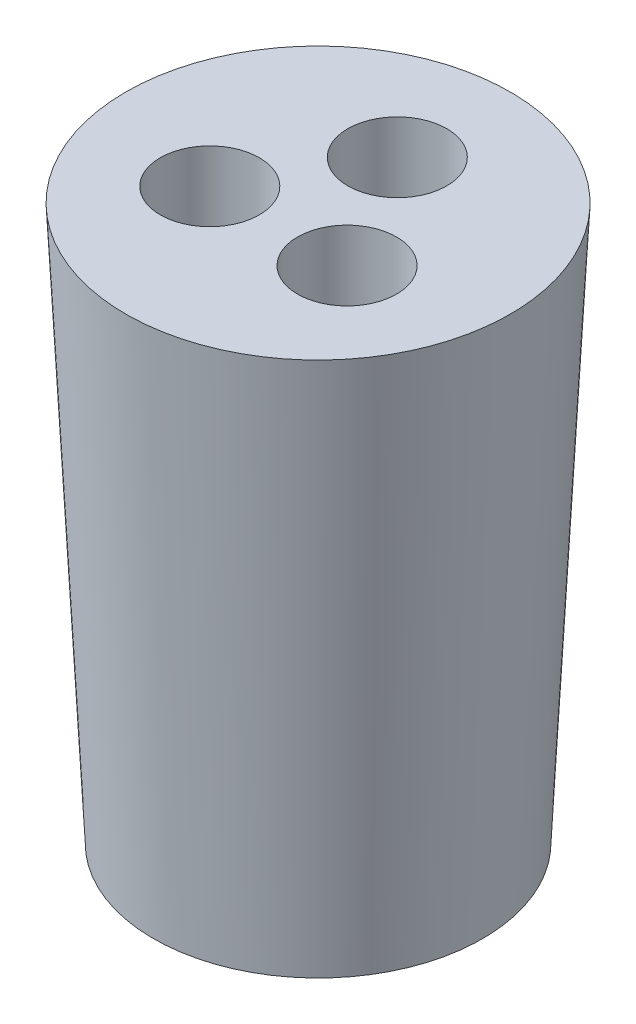
SolidWorks part; units mm, degrees
ref_plane "Front Plane" through (0, 0, 0) normal (0, 0, 1) x (1, 0, 0)
ref_plane "Top Plane" through (0, 0, 0) normal (0, 1, 0) x (1, 0, 0)
ref_plane "Right Plane" through (0, 0, 0) normal (1, 0, 0) x (0, 0, -1)
sketch "Sketch1" plane through (0, 0, 0) normal (0, 0, 1) x (1, 0, 0)
  line L0 (10.55, 0) -> (12.328, 35.56)
  line L1 (12.328, 35.56) -> (0, 35.56)
  line L2 (0, 35.56) -> (0, 0)
  line L3 (0, 0) -> (10.55, 0)
  dimension "D1" = 35.56
  dimension "D2" = 10.55
  dimension "D4" = 92.862
revolve "Revolve1" add sketch "Sketch1" angle 360 about L2
sketch "Sketch2" plane through (0, 35.56, 0) normal (0, 1, 0) x (1, 0, 0)
  circle A0 centre (0, 5.08) radius 3.175
  circle A1 centre (4.3994, -2.54) radius 3.175
  circle A2 centre (-4.3994, -2.54) radius 3.175
  point P8 (0, 0)
  dimension "D1" = 6.35
  dimension "D3" = 5.08
  dimension "D2" = 3
extrude "Cut-Extrude1" cut sketch "Sketch2" against normal through all both contours A2
